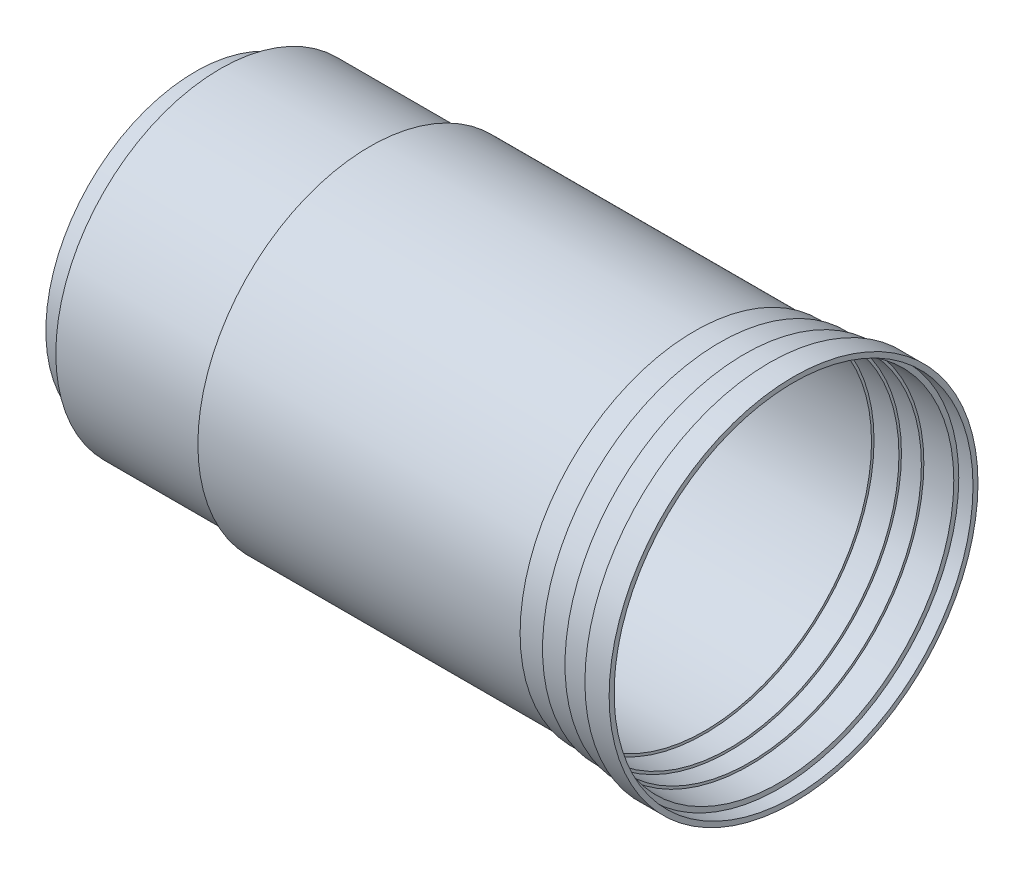
SolidWorks part; units mm, degrees
ref_plane "Plan de face" through (0, 0, 0) normal (0, 0, 1) x (1, 0, 0)
ref_plane "Plan de dessus" through (0, 0, 0) normal (0, 1, 0) x (1, 0, 0)
ref_plane "Plan de droite" through (0, 0, 0) normal (1, 0, 0) x (0, 0, -1)
sketch "Esquisse1" plane through (0, 0, 0) normal (0, 0, 1) x (1, 0, 0)
  line L0 (0, 0) -> (-120, 0) construction
  line L1 (-120, 0) -> (-120, 30)
  line L2 (0, 37) -> (-4.8573, 37)
  line L3 (-4.8573, 37) -> (-4.8573, 36)
  line L4 (-120, 30) -> (-115, 30)
  line L5 (-115, 30) -> (-115, 33)
  line L6 (-115, 33) -> (-85, 33)
  line L7 (-19.8573, 34.5) -> (-85, 34.5)
  line L8 (-85, 34.5) -> (-85, 33)
  line L9 (-119, 0) -> (-119, 29)
  line L10 (-4.8573, 36) -> (-9.8573, 36)
  line L11 (-9.8573, 36) -> (-9.8573, 35.5)
  line L12 (-9.8573, 35.5) -> (-14.8573, 35.5)
  line L13 (-14.8573, 35.5) -> (-14.8573, 35)
  line L14 (-14.8573, 35) -> (-19.8573, 35)
  line L15 (-119, 29) -> (-114, 29)
  line L16 (-19.8573, 35) -> (-19.8573, 34.5)
  line L17 (-114, 29) -> (-114, 32)
  line L18 (-114, 32) -> (-84, 32)
  line L19 (-84, 32) -> (-84, 33.5)
  line L20 (-84, 33.5) -> (-17.8573, 33.5)
  line L21 (-17.8573, 33.5) -> (-17.8573, 34)
  line L22 (-17.8573, 34) -> (-12.8573, 34)
  line L23 (-12.8573, 34) -> (-12.8573, 34.5)
  line L24 (-12.8573, 34.5) -> (-8.8631, 34.5)
  line L25 (-8.8631, 34.5) -> (-8.8631, 35)
  line L26 (-8.8631, 35) -> (-2.8573, 35)
  line L27 (-2.8573, 35) -> (-2.8573, 36)
  line L28 (-2.8573, 36) -> (0, 36)
  line L29 (0, 36) -> (0, 37)
  line L30 (-120, 0) -> (-119, 0)
  point P31 (-14.8573, 35.25)
  point P33 (-19.8573, 34.75)
  dimension "D1" = 120
  dimension "D2" = 30
  dimension "D4" = 5
  dimension "D5" = 3
  dimension "D6" = 30
  dimension "D7" = 65.1427
  dimension "D8" = 1
  dimension "D9" = 5
  dimension "D10" = 0.5
  dimension "D11" = 5
  dimension "D12" = 0.5
  dimension "D13" = 5
  dimension "D14" = 0.5
  dimension "D15" = 1
  dimension "D16" = 1
  dimension "D17" = 37
  dimension "D18" = 4.8573
  dimension "D19" = 8.8631
  dimension "D20" = 2
  dimension "D21" = 1
  dimension "D22" = 1
  dimension "D23" = 1
  dimension "D24" = 1
  dimension "D25" = 1
  dimension "D26" = 1
  dimension "D27" = 1
  dimension "D28" = 1
  dimension "D29" = 2
  dimension "D30" = 2
revolve "Révolution1" add sketch "Esquisse1" angle 360 about L0
